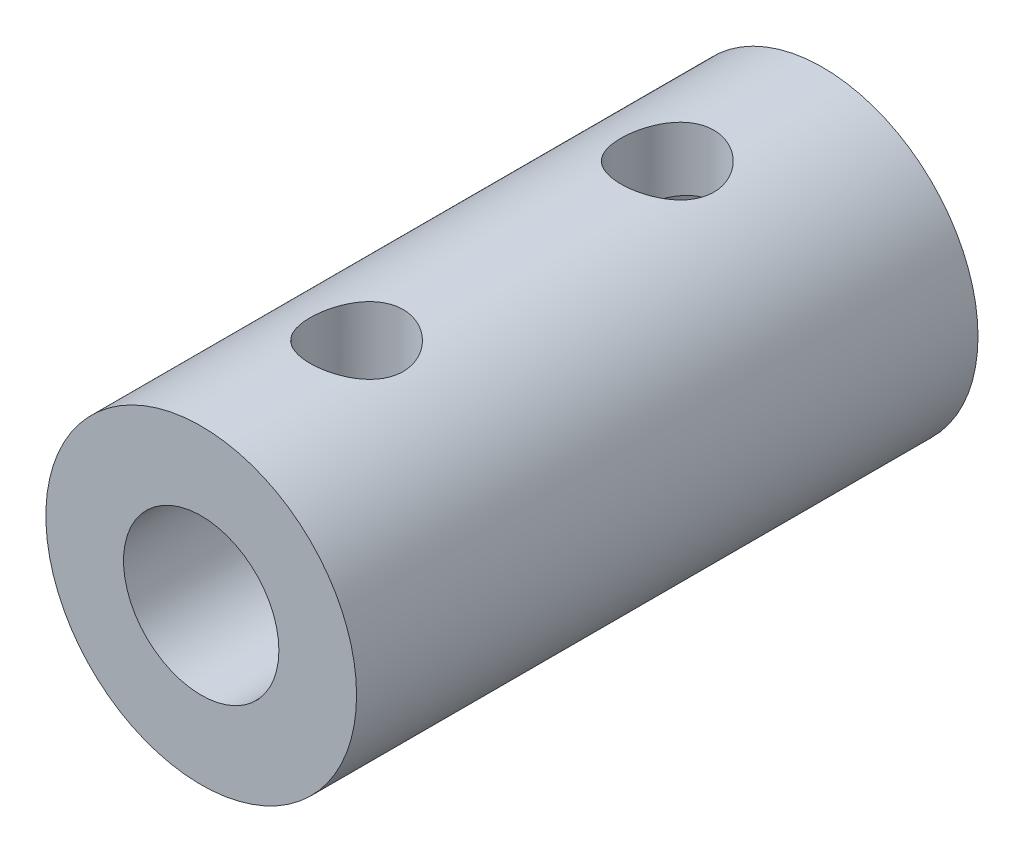
SolidWorks part; units mm, degrees
ref_plane "Front Plane" through (0, 0, 0) normal (0, 0, 1) x (1, 0, 0)
ref_plane "Top Plane" through (0, 0, 0) normal (0, 1, 0) x (1, 0, 0)
ref_plane "Right Plane" through (0, 0, 0) normal (1, 0, 0) x (0, 0, -1)
sketch "Sketch1" plane through (0, 0, 0) normal (0, 0, 1) x (1, 0, 0)
  circle A0 centre (0, 0) radius 3
  circle A1 centre (0, 0) radius 5
  dimension "D1" = 6
  dimension "D2" = 2
extrude "Boss-Extrude1" add sketch "Sketch1" along normal blind 10
sketch "Sketch2" plane through (0, 0, 10) normal (0, 0, 1) x (1, 0, 0)
  circle A0 centre (0, 0) radius 2.5
  circle A1 centre (0, 0) radius 5
  dimension "D1" = 5
extrude "Boss-Extrude2" add sketch "Sketch2" along normal blind 10
sketch "Sketch3" plane through (0, 0, 0) normal (0, 1, 0) x (1, 0, 0)
  line L0 (0, 0) -> (0, -20) construction
  line L1 (3, 0) -> (-3, 0) construction
  line L2 (-5, -20) -> (5, -20) construction
  circle A0 centre (0, -5) radius 1.5
  circle A1 centre (0, -15) radius 1.5
  dimension "D1" = 3
  dimension "D2" = 3
  dimension "D3" = 5
  dimension "D4" = 5
extrude "Cut-Extrude1" cut sketch "Sketch3" along normal blind 10
